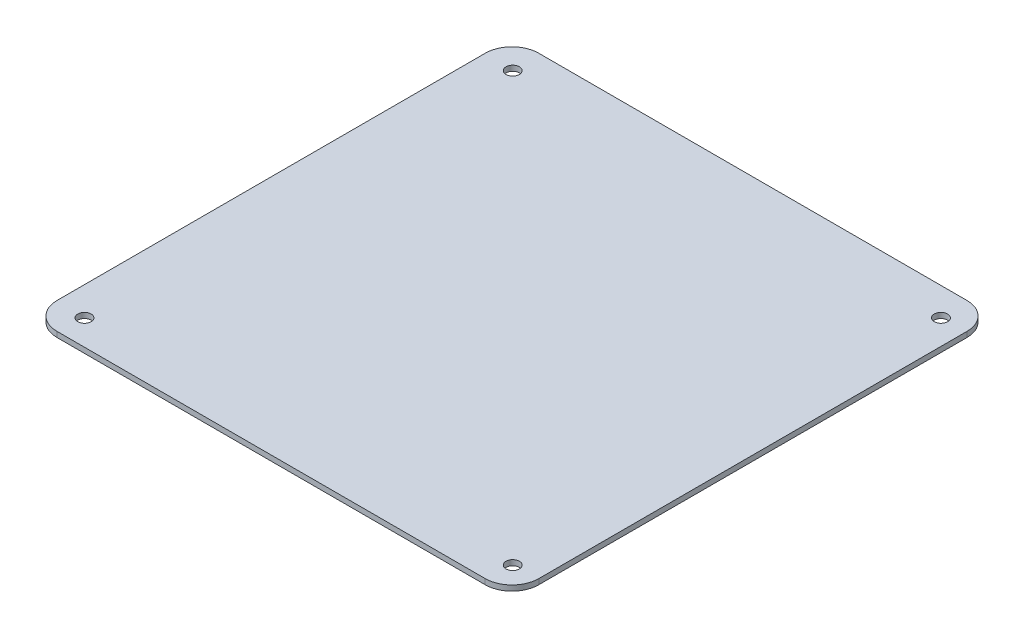
SolidWorks part; units mm, degrees
ref_plane "Front" through (0, 0, 0) normal (0, 0, 1) x (1, 0, 0)
ref_plane "Top" through (0, 0, 0) normal (0, 1, 0) x (1, 0, 0)
ref_plane "Right" through (0, 0, 0) normal (1, 0, 0) x (0, 0, -1)
sketch "Sketch1" plane through (0, 0, 0) normal (0, 1, 0) x (1, 0, 0)
  line L1 (-101.7464, 60.8824) -> (78.2536, 60.8824)
  line L2 (-101.7464, 60.8824) -> (-101.7464, -119.1176)
  line L3 (-101.7464, -119.1176) -> (78.2536, -119.1176)
  line L4 (78.2536, 60.8824) -> (78.2536, -119.1176)
  circle A0 centre (-90.9856, 50.388) radius 2.5
  circle A1 centre (69.0144, 50.388) radius 2.5
  circle A2 centre (-90.9856, -109.612) radius 2.5
  circle A3 centre (69.0144, -109.612) radius 2.5
  point P12 (0, 0)
  point P13 (-126.5019, 66.8159)
  point P14 (33.4982, -93.9051)
  point P15 (0, 0)
  point P16 (0, 0)
  point P17 (-12.7493, -69.2545)
  point P18 (0, 0)
  point P19 (69.9462, -108.9931)
  point P20 (-92.0782, 52.213)
  point P21 (-91.3508, 52.2707)
  point P22 (-90.9856, -109.612)
  dimension "D5" = 160
  dimension "D1" = 180
  dimension "D2" = 180
  dimension "D3" = 160
  dimension "D4" = 160
extrude "Boss-Extrude1" add sketch "Sketch1" along normal blind 2
fillet "Fillet1" radius 10 4 edges at (-101.7464, 1, -60.8824) (-101.7464, 1, 119.1176) (78.2536, 1, -60.8824) (78.2536, 1, 119.1176)
